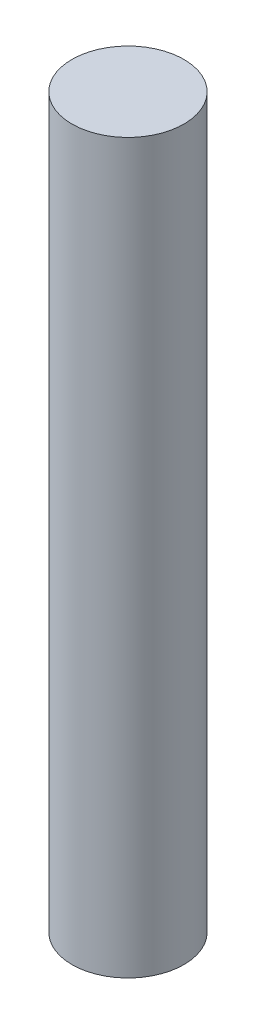
SolidWorks part; units mm, degrees
ref_plane "Front Plane" through (0, 0, 0) normal (0, 0, 1) x (1, 0, 0)
ref_plane "Top Plane" through (0, 0, 0) normal (0, 1, 0) x (1, 0, 0)
ref_plane "Right Plane" through (0, 0, 0) normal (1, 0, 0) x (0, 0, -1)
sketch "Sketch1" plane through (0, 0, 0) normal (0, 1, 0) x (1, 0, 0)
  circle A0 centre (0, 0) radius 152.4
extrude "Boss-Extrude1" add sketch "Sketch1" along normal blind 1981.2
sketch "Sketch2" plane through (0, 1981.2, 0) normal (0, 1, 0) x (1, 0, 0)
  line L0 (0, 152.4) -> (0, -152.4)
  circle A0 centre (0, 0) radius 152.4 construction
sketch "Sketch3" plane through (0, 0, 0) normal (0, -1, 0) x (1, 0, 0)
  line L0 (0, 152.4) -> (0, -152.4)
  circle A0 centre (0, 0) radius 152.4 construction
